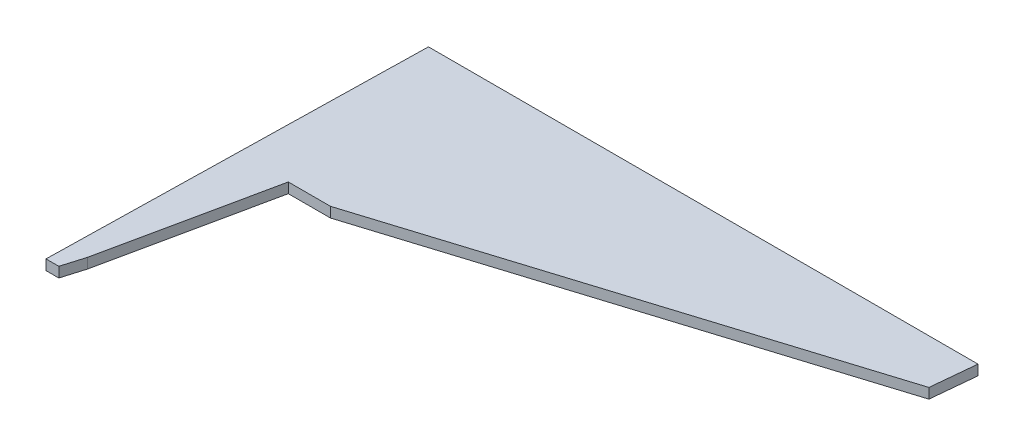
SolidWorks part; units mm, degrees
ref_plane "Plan de face" through (0, 0, 0) normal (0, 0, 1) x (1, 0, 0)
ref_plane "Plan de dessus" through (0, 0, 0) normal (0, 1, 0) x (1, 0, 0)
ref_plane "Plan de droite" through (0, 0, 0) normal (1, 0, 0) x (0, 0, -1)
sketch "Esquisse1" plane through (0, 0, 0) normal (0, 1, 0) x (1, 0, 0)
  line L0 (1.4946, 73.6789) -> (0, 0)
  line L1 (0, 0) -> (2.5195, 0)
  line L2 (2.5195, 0) -> (3.8089, 4.3265)
  line L3 (3.8089, 4.3265) -> (10.7222, 36.905)
  line L4 (10.7222, 36.905) -> (19.0036, 36.905)
  line L5 (19.0036, 36.905) -> (108.6456, 64.8882)
  line L6 (108.6456, 64.8882) -> (109.503, 73.6789)
  line L7 (109.503, 73.6789) -> (1.4946, 73.6789)
  point P8 (0, 0)
extrude "Boss.-Extru.1" add sketch "Esquisse1" along normal blind 2
